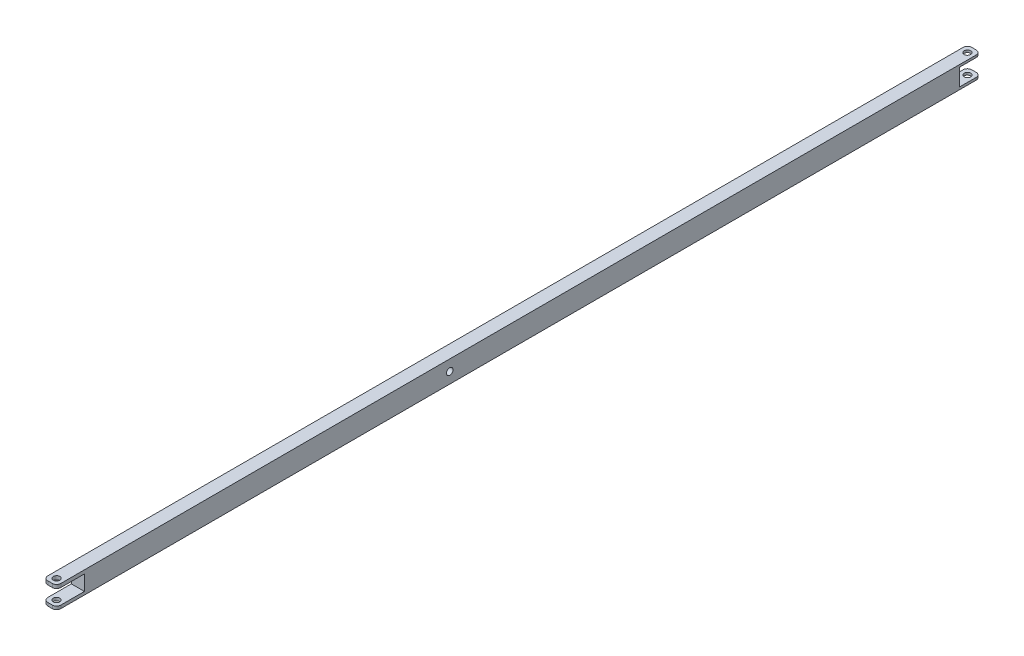
SolidWorks part; units mm, degrees
material "6063-T6"
ref_plane "Front Plane" through (0, 0, 0) normal (0, 0, 1) x (1, 0, 0)
ref_plane "Top Plane" through (0, 0, 0) normal (0, 1, 0) x (1, 0, 0)
ref_plane "Right Plane" through (0, 0, 0) normal (1, 0, 0) x (0, 0, -1)
sketch "Sketch1" plane through (0, 0, 0) normal (0, 0, 1) x (1, 0, 0)
  line L1 (0, 0) -> (7.62, 0)
  line L2 (0, 0) -> (0, 12.7)
  line L3 (0, 12.7) -> (7.62, 12.7)
  line L4 (7.62, 0) -> (7.62, 12.7)
  dimension "D1" = 7.62
  dimension "D2" = 12.7
extrude "Boss-Extrude1" add sketch "Sketch1" along normal blind 457.2
sketch "Sketch2" plane through (7.62, 0, 0) normal (1, 0, 0) x (0, 0, -1)
  line L0 (-457.2, 12.7) -> (0, 12.7) construction
  circle A0 centre (-7.3361, 12.45) radius 0.075
  dimension "D1" = 0.15
  dimension "D2" = 0.25
sketch "Sketch3" plane through (7.62, 0, 0) normal (1, 0, 0) x (0, 0, -1)
  line L0 (-457.2, 12.7) -> (0, 12.7) construction
  line L1 (-457.2, 0) -> (0, 0) construction
  line L2 (0, 0) -> (0, 12.7) construction
  line L3 (-457.2, 0) -> (-457.2, 12.7) construction
  circle A0 centre (-228.6, 6.35) radius 1.905
  dimension "D1" = 3.81
  dimension "D2" = 6.35
  dimension "D3" = 6.35
  dimension "D4" = 228.6
  dimension "D5" = 228.6
extrude "Cut-Extrude2" cut sketch "Sketch3" against normal blind 15
sketch "Sketch4" plane through (7.62, 0, 0) normal (1, 0, 0) x (0, 0, -1)
  line L0 (-457.2, 0) -> (-457.2, 12.7) construction
  line L1 (-457.2, 10.6365) -> (-441.013, 10.6365)
  line L2 (-457.2, 10.6365) -> (-457.2, 1.816)
  line L3 (-457.2, 1.816) -> (-441.013, 1.816)
  line L4 (-441.013, 10.6365) -> (-441.013, 1.816)
extrude "Cut-Extrude3" cut sketch "Sketch4" against normal blind 15
sketch "Sketch5" plane through (0, 12.7, 0) normal (0, 1, 0) x (1, 0, 0)
  line L0 (0, -457.2) -> (7.62, -449.58)
  line L1 (7.62, -457.2) -> (7.62, 0) construction
  circle A0 centre (3.81, -453.39) radius 1.9059
extrude "Cut-Extrude4" cut sketch "Sketch5" against normal blind 15 contours L0 A0 | L0 A0
fillet "Fillet1" radius 2.5 4 edges at (0, 0.908, 457.2) (7.62, 0.908, 457.2) (7.62, 11.6682, 457.2) (0, 11.6682, 457.2)
sketch "Sketch6" plane through (0, 0, 0) normal (0, 0, -1) x (-1, 0, 0)
  line L4 (0, 0) -> (0, 12.7)
  line L5 (0, 12.7) -> (-7.62, 12.7)
  line L6 (-7.62, 12.7) -> (-7.62, 0)
  line L7 (-7.62, 0) -> (0, 0)
  line L8 (0, 0) -> (0, 12.7)
  line L9 (0, 12.7) -> (-7.62, 12.7)
  line L10 (-7.62, 12.7) -> (-7.62, 0)
  line L11 (-7.62, 0) -> (0, 0)
  dimension "D1" = 0
extrude "Boss-Extrude2" add sketch "Sketch6" along normal blind 80
sketch "Sketch7" plane through (7.62, 0, 0) normal (1, 0, 0) x (0, 0, -1)
  line L0 (80, 12.7) -> (80, 0) construction
  line L1 (80, 11.3649) -> (67.8669, 11.3649)
  line L2 (80, 11.3649) -> (80, 1.4267)
  line L3 (80, 1.4267) -> (67.8669, 1.4267)
  line L4 (67.8669, 11.3649) -> (67.8669, 1.4267)
extrude "Cut-Extrude5" cut sketch "Sketch7" against normal blind 80
sketch "Sketch8" plane through (0, 12.7, 0) normal (0, 1, 0) x (1, 0, 0)
  line L0 (0, 80) -> (7.62, 72.38)
  line L1 (7.62, -454.7) -> (7.62, 80) construction
  circle A1 centre (3.8916, 76.1084) radius 1.905
  dimension "D1" = 3.81
extrude "Cut-Extrude6" cut sketch "Sketch8" against normal blind 80 contours L0 A1 | L0 A1
fillet "Fillet2" radius 2.5 4 edges at (0, 12.0324, -80) (7.62, 12.0324, -80) (7.62, 0.7133, -80) (0, 0.7133, -80)
